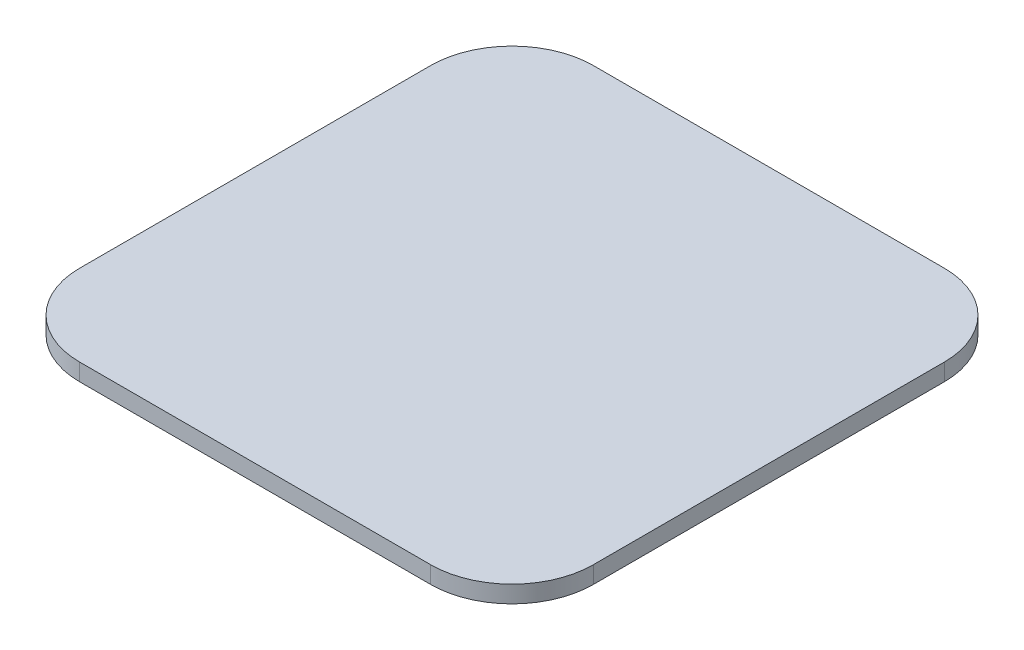
SolidWorks part; units mm, degrees
ref_plane "Front Plane" through (0, 0, 0) normal (0, 0, 1) x (1, 0, 0)
ref_plane "Top Plane" through (0, 0, 0) normal (0, 1, 0) x (1, 0, 0)
ref_plane "Right Plane" through (0, 0, 0) normal (1, 0, 0) x (0, 0, -1)
sketch "Sketch1" plane through (0, 0, 0) normal (0, 1, 0) x (1, 0, 0)
  line L1 (0, 0) -> (120, 0)
  line L2 (0, 0) -> (0, 120)
  line L3 (0, 120) -> (120, 120)
  line L4 (120, 0) -> (120, 120)
  dimension "D1" = 120
extrude "Boss-Extrude1" add sketch "Sketch1" along normal blind 4
fillet "Fillet1" radius 19 4 edges at (0, 2, -120) (120, 2, -120) (120, 2, 0) (0, 2, 0)
